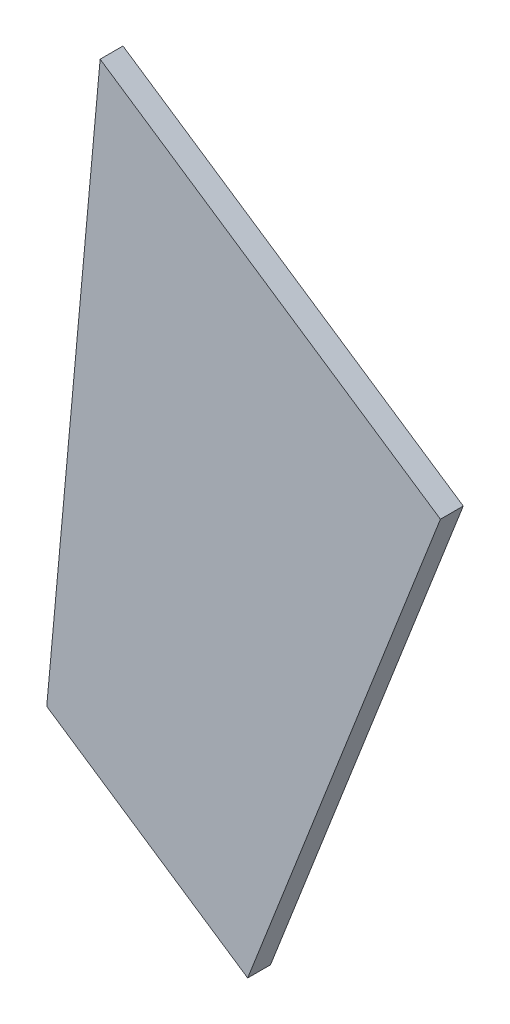
SolidWorks part; units mm, degrees
ref_plane "Front Plane" through (0, 0, 0) normal (0, 0, 1) x (1, 0, 0)
ref_plane "Top Plane" through (0, 0, 0) normal (0, 1, 0) x (1, 0, 0)
ref_plane "Right Plane" through (0, 0, 0) normal (1, 0, 0) x (0, 0, -1)
sketch "Sketch1" plane through (0, 0, 0) normal (0, 0, 1) x (1, 0, 0)
  line L0 (-7.0187, -77.1734) -> (0, 0)
  line L1 (-7.0187, -77.1734) -> (19.3895, -94.8876)
  line L2 (0, 0) -> (44.7238, -30)
  line L3 (19.3895, -94.8876) -> (44.7238, -30)
  point P4 (0, 0)
  dimension "D1" = 68
  dimension "D2" = 31.7992
  dimension "D3" = 69.6579
extrude "Boss-Extrude1" add sketch "Sketch1" along normal blind 3
